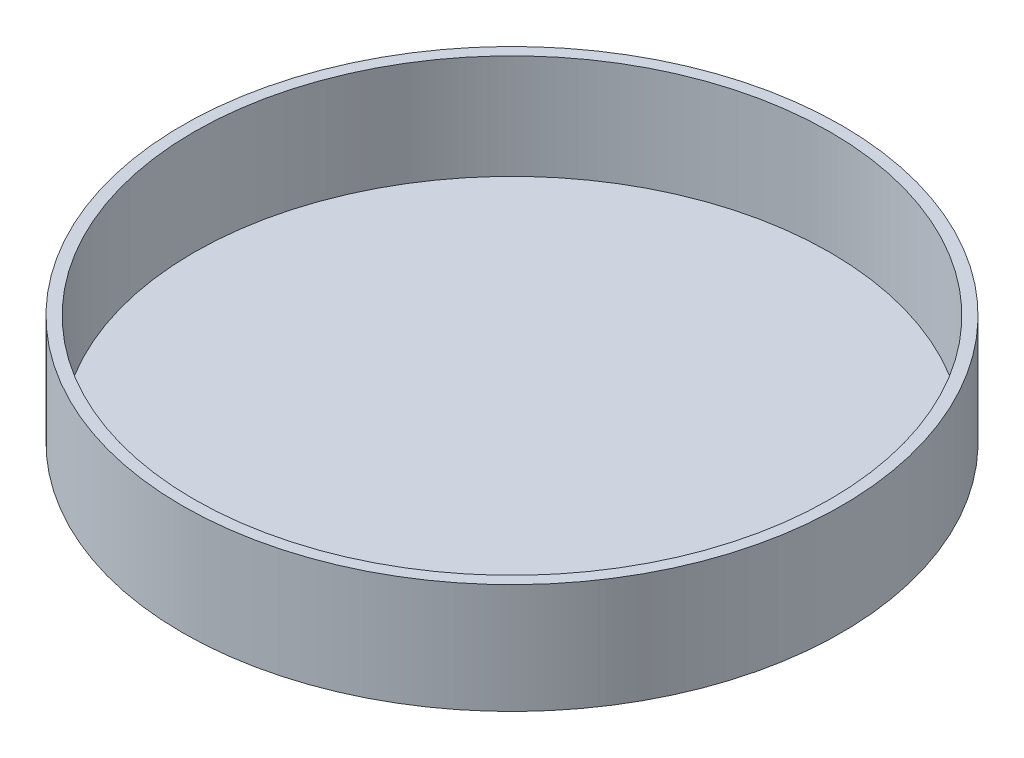
SolidWorks part; units mm, degrees
material "PVC Rigid"
ref_plane "Front Plane" through (0, 0, 0) normal (0, 0, 1) x (1, 0, 0)
ref_plane "Top Plane" through (0, 0, 0) normal (0, 1, 0) x (1, 0, 0)
ref_plane "Right Plane" through (0, 0, 0) normal (1, 0, 0) x (0, 0, -1)
sketch "Sketch1" plane through (0, 0, 0) normal (0, 1, 0) x (1, 0, 0)
  circle A0 centre (0, 0) radius 152.4
  circle A1 centre (0, 0) radius 147.106
  dimension "D1" = 304.8
extrude "Boss-Extrude1" add sketch "Sketch1" along normal blind 50.8
sketch "Sketch3" plane through (0, 0, 0) normal (0, -1, 0) x (1, 0, 0)
  circle A0 centre (0, 0) radius 147.106
extrude "Boss-Extrude2" add sketch "Sketch3" against normal blind 2.54 separate body
